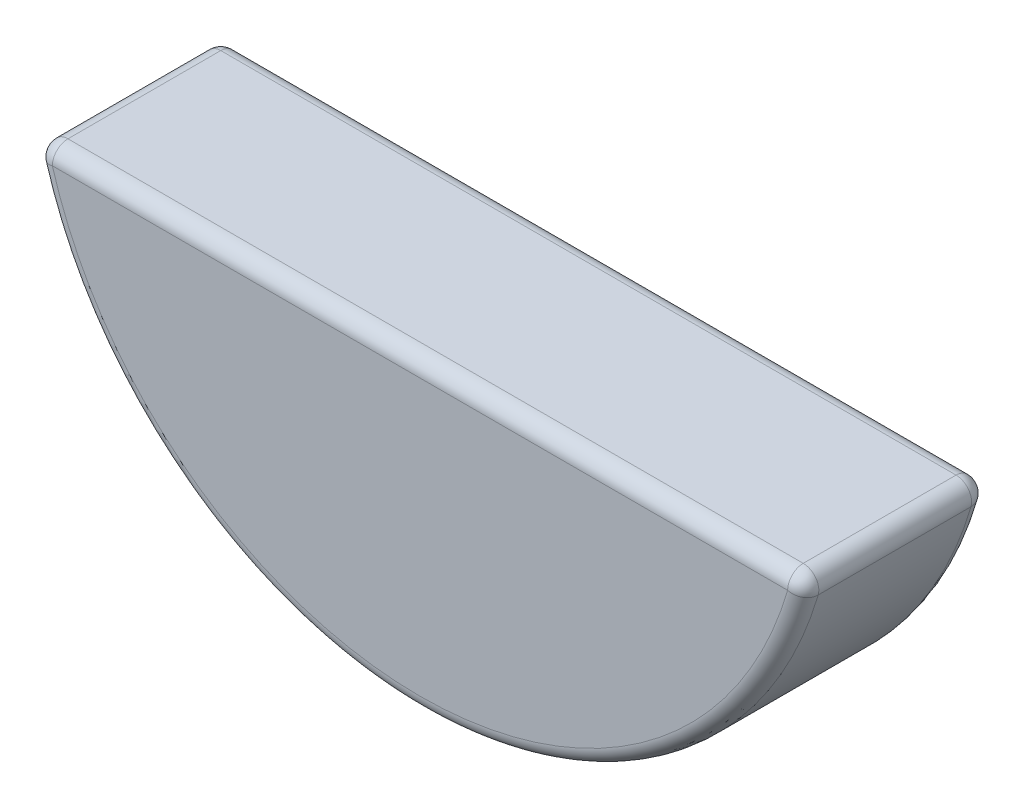
SolidWorks part; units mm, degrees
ref_plane "Front Plane" through (0, 0, 0) normal (0, 0, 1) x (1, 0, 0)
ref_plane "Top Plane" through (0, 0, 0) normal (0, 1, 0) x (1, 0, 0)
ref_plane "Right Plane" through (0, 0, 0) normal (1, 0, 0) x (0, 0, -1)
sketch "Sketch1" plane through (0, 0, 0) normal (0, 0, 1) x (1, 0, 0)
  line L1 (-6.325, -1.4981) -> (6.325, -1.4981)
  line L4 (0, 0) -> (0, -1.4981) construction
  line L5 (0, -6.5) -> (0, -1.4981) construction
  line L6 (-6.5, 0) -> (6.5, 0) construction
  arc A1 (-6.325, -1.4981) -> (6.325, -1.4981) centre (0, 0) ccw
  circle A3 centre (0, 0) radius 6.5 construction
  dimension "Full Dia." = 13
  dimension "Length" = 12.65
  dimension "Height" = 5.0019
extrude "Extrude1" add sketch "Sketch1" along normal mid plane 3
fillet "Fillet1" radius 0.254 6 edges at (0, -6.5, -1.5) (0, -6.5, 1.5) (0, -1.4981, -1.5) (0, -1.4981, 1.5) (-6.325, -1.4981, 0) (6.325, -1.4981, 0)
